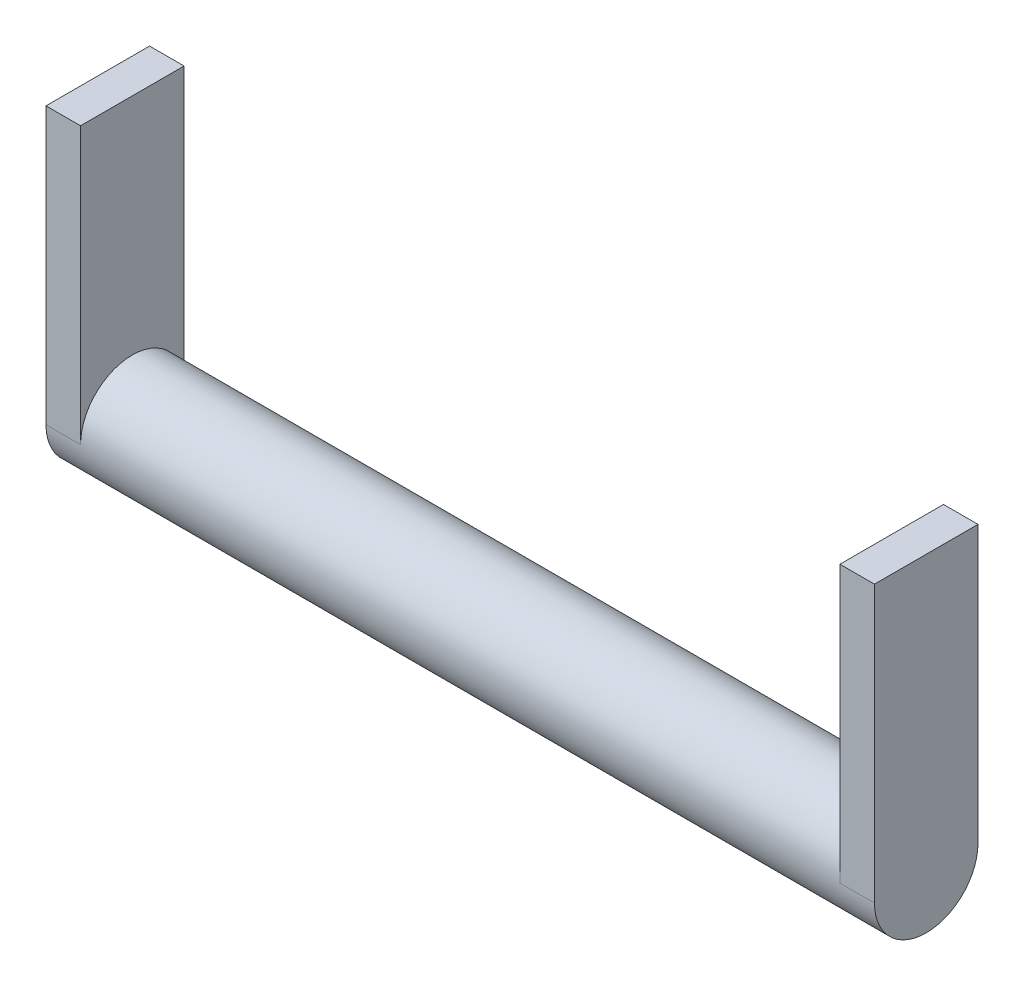
SolidWorks part; units mm, degrees
ref_plane "Front Plane" through (0, 0, 0) normal (0, 0, 1) x (1, 0, 0)
ref_plane "Top Plane" through (0, 0, 0) normal (0, 1, 0) x (1, 0, 0)
ref_plane "Right Plane" through (0, 0, 0) normal (1, 0, 0) x (0, 0, -1)
sketch "Sketch2" plane through (0, 0, 0) normal (1, 0, 0) x (0, 0, -1)
  circle A0 centre (0, 0) radius 38.1
extrude "Boss-Extrude1" add sketch "Sketch2" along normal blind 279.4
sketch "Sketch3" plane through (279.4, 0, 0) normal (1, 0, 0) x (0, 0, -1)
  line L0 (-38.1, 0) -> (-38.1, 203.2)
  line L1 (-38.1, 203.2) -> (38.1, 203.2)
  line L2 (38.1, 203.2) -> (38.1, 0)
  circle A0 centre (0, 0) radius 38.1 construction
  arc A1 (38.1, 0) -> (-38.1, 0) centre (0, 0) cw
  point P8 (0, 0)
extrude "Boss-Extrude2" add sketch "Sketch3" along normal blind 25.4
mirror "Mirror1" about plane through (0, 0, 0) normal (1, 0, 0) of "Boss-Extrude2", "Boss-Extrude1"
